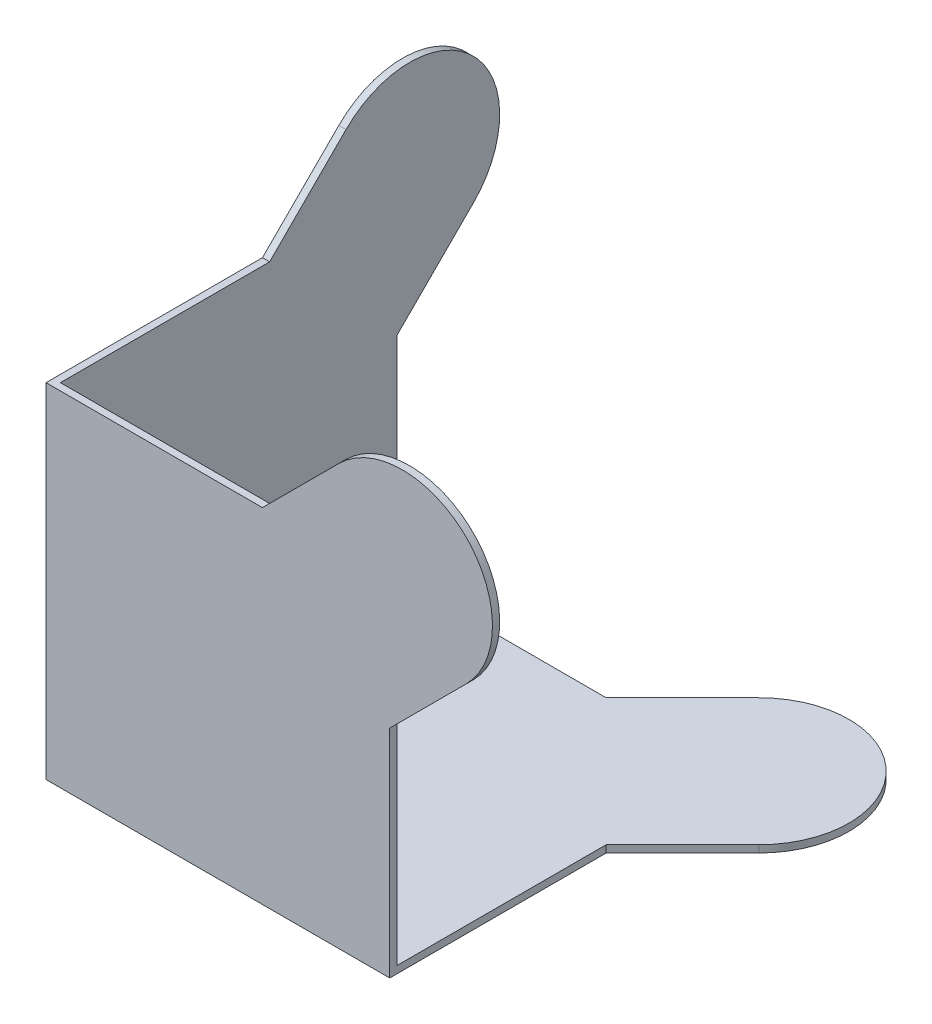
SolidWorks part; units mm, degrees
material "6063-O"
ref_plane "Front Plane" through (0, 0, 0) normal (0, 0, 1) x (1, 0, 0)
ref_plane "Top Plane" through (0, 0, 0) normal (0, 1, 0) x (1, 0, 0)
ref_plane "Right Plane" through (0, 0, 0) normal (1, 0, 0) x (0, 0, -1)
sketch "Sketch1" plane through (0, 0, 0) normal (0, 0, 1) x (1, 0, 0)
  line L0 (30.0546, 47.7322) -> (40.6612, 58.3388)
  line L1 (0, 0) -> (47.7322, 0)
  line L2 (0, 0) -> (0, 47.7322)
  line L3 (0, 47.7322) -> (30.0546, 47.7322)
  line L4 (47.7322, 0) -> (47.7322, 30.0546)
  line L5 (58.3388, 40.6612) -> (47.7322, 30.0546)
  line L6 (49.5, 49.5) -> (0, 0) construction
  arc A0 (40.6612, 58.3388) -> (58.3388, 40.6612) centre (49.5, 49.5) cw
  dimension "D1" = 45
  dimension "D2" = 62
  dimension "D3" = 25
  dimension "D4" = 15
extrude "Boss-Extrude1" add sketch "Sketch1" against normal blind 1
sketch "Sketch2" plane through (0, 0, 0) normal (1, 0, 0) x (0, 0, -1)
  line L0 (30.0546, 47.7322) -> (40.6612, 58.3388)
  line L1 (0, 0) -> (47.7322, 0)
  line L2 (0, 0) -> (0, 47.7322)
  line L3 (0, 47.7322) -> (30.0546, 47.7322)
  line L4 (47.7322, 0) -> (47.7322, 30.0546)
  line L5 (58.3388, 40.6612) -> (47.7322, 30.0546)
  line L6 (0, 0) -> (49.5, 49.5) construction
  arc A0 (40.6612, 58.3388) -> (58.3388, 40.6612) centre (49.5, 49.5) cw
  dimension "D1" = 62
  dimension "D2" = 25
  dimension "D3" = 15
  dimension "D4" = 45
extrude "Boss-Extrude2" add sketch "Sketch2" along normal blind 1
sketch "Sketch3" plane through (0, 0, 0) normal (0, 1, 0) x (1, 0, 0)
  line L0 (30.0546, 47.7322) -> (40.6612, 58.3388)
  line L1 (0, 0) -> (47.7322, 0)
  line L2 (0, 0) -> (0, 47.7322)
  line L3 (0, 47.7322) -> (30.0546, 47.7322)
  line L4 (47.7322, 0) -> (47.7322, 30.0546)
  line L5 (58.3388, 40.6612) -> (47.7322, 30.0546)
  line L6 (0, 0) -> (49.5, 49.5) construction
  arc A0 (40.6612, 58.3388) -> (58.3388, 40.6612) centre (49.5, 49.5) cw
  dimension "D1" = 45
  dimension "D2" = 62
  dimension "D3" = 25
  dimension "D4" = 15
extrude "Boss-Extrude3" add sketch "Sketch3" along normal blind 1
equation "\"A\"= 62"
equation "\"B\"= 25"
equation "\"C\"= 15"
equation "\"D2@Sketch1\"=\"A\""
equation "\"D3@Sketch1\"=\"B\""
equation "\"D4@Sketch1\"=\"C\""
equation "\"D1@Sketch2\"=\"A\""
equation "\"D2@Sketch2\"=\"B\""
equation "\"D3@Sketch2\"=\"C\""
equation "\"D\"= 1"
equation "\"D1@Boss-Extrude1\"=\"D\""
equation "\"D1@Boss-Extrude2\"=\"D\""
equation "\"D2@Sketch3\"=\"A\""
equation "\"D3@Sketch3\"=\"B\""
equation "\"D4@Sketch3\"=\"C\""
equation "\"D1@Boss-Extrude3\"=\"D\""
